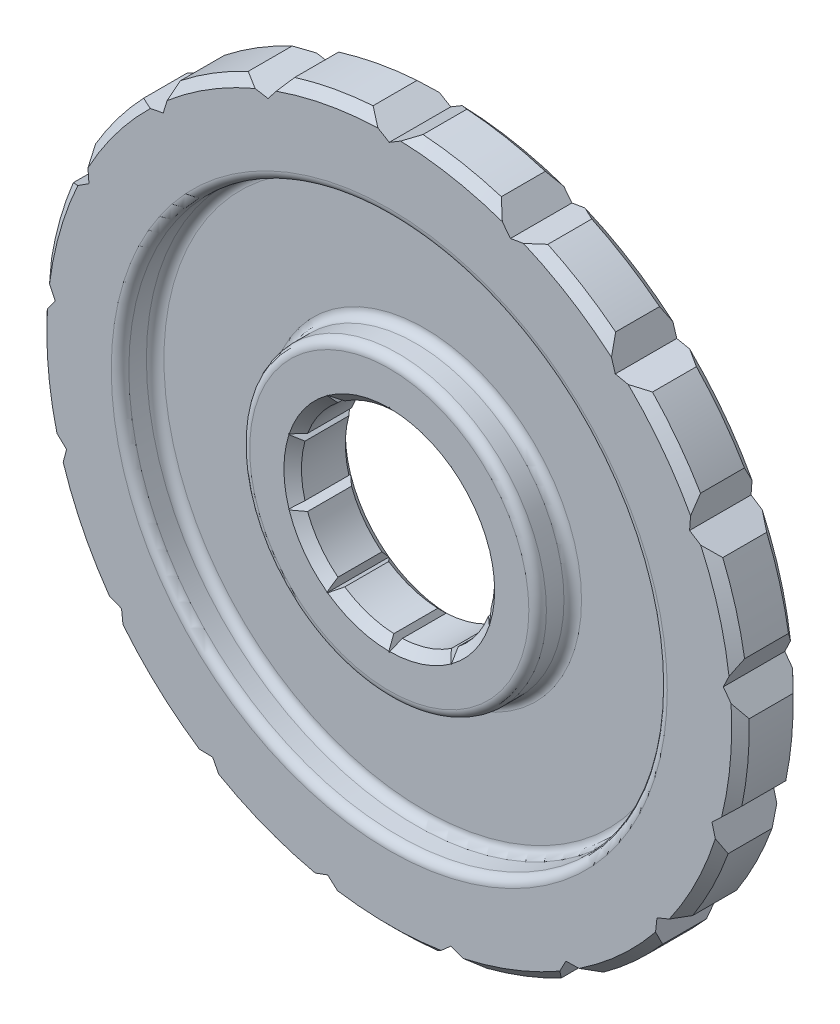
SolidWorks part; units mm, degrees
ref_plane "Front Plane" through (0, 0, 0) normal (0, 0, 1) x (1, 0, 0)
ref_plane "Top Plane" through (0, 0, 0) normal (0, 1, 0) x (1, 0, 0)
ref_plane "Right Plane" through (0, 0, 0) normal (1, 0, 0) x (0, 0, -1)
sketch "Sketch1" plane through (0, 0, 0) normal (0, 0, 1) x (1, 0, 0)
  circle A0 centre (0, 0) radius 11
  circle A1 centre (0, 0) radius 40
  dimension "D1" = 22
  dimension "D2" = 80
extrude "Boss-Extrude1" add sketch "Sketch1" along normal blind 7
chamfer "Chamfer1" distance 1 angle 45 4 edges at (40, 0, 0) (40, 0, 7) (11, 0, 0) (11, 0, 7)
sketch "Sketch2" plane through (0, 0, 7) normal (0, 0, 1) x (1, 0, 0)
  line L0 (0, 0) -> (0, 34.5062) construction
  line L1 (0, 12.1033) -> (-0.887, 10.0504)
  line L2 (-0.887, 10.0504) -> (0.887, 10.0504)
  line L3 (0.887, 10.0504) -> (0, 12.1033)
  line L4 (6.6251, 7.6096) -> (7.1141, 9.7917)
  line L5 (7.1141, 9.7917) -> (5.1899, 8.6523)
  line L6 (5.1899, 8.6523) -> (6.6251, 7.6096)
  line L7 (9.8326, 2.2622) -> (11.5109, 3.7401)
  line L8 (11.5109, 3.7401) -> (9.2844, 3.9493)
  line L9 (9.2844, 3.9493) -> (9.8326, 2.2622)
  line L10 (9.2844, -3.9493) -> (11.5109, -3.7401)
  line L11 (11.5109, -3.7401) -> (9.8326, -2.2622)
  line L12 (9.8326, -2.2622) -> (9.2844, -3.9493)
  line L13 (5.1899, -8.6523) -> (7.1141, -9.7917)
  line L14 (7.1141, -9.7917) -> (6.6251, -7.6096)
  line L15 (6.6251, -7.6096) -> (5.1899, -8.6523)
  line L16 (-0.887, -10.0504) -> (0, -12.1033)
  line L17 (0, -12.1033) -> (0.887, -10.0504)
  line L18 (0.887, -10.0504) -> (-0.887, -10.0504)
  line L19 (-6.6251, -7.6096) -> (-7.1141, -9.7917)
  line L20 (-7.1141, -9.7917) -> (-5.1899, -8.6523)
  line L21 (-5.1899, -8.6523) -> (-6.6251, -7.6096)
  line L22 (-9.8326, -2.2622) -> (-11.5109, -3.7401)
  line L23 (-11.5109, -3.7401) -> (-9.2844, -3.9493)
  line L24 (-9.2844, -3.9493) -> (-9.8326, -2.2622)
  line L25 (-9.2844, 3.9493) -> (-11.5109, 3.7401)
  line L26 (-11.5109, 3.7401) -> (-9.8326, 2.2622)
  line L27 (-9.8326, 2.2622) -> (-9.2844, 3.9493)
  line L28 (-5.1899, 8.6523) -> (-7.1141, 9.7917)
  line L29 (-7.1141, 9.7917) -> (-6.6251, 7.6096)
  line L30 (-6.6251, 7.6096) -> (-5.1899, 8.6523)
  line L31 (-4.9611, 41.1614) -> (0, 38.2086)
  line L32 (0, 38.2086) -> (4.9611, 41.1614)
  line L33 (4.9611, 41.1614) -> (-4.9611, 41.1614)
  line L34 (19.4954, 36.5897) -> (10.2431, 40.1741)
  line L35 (10.2431, 40.1741) -> (13.8025, 35.6284)
  line L36 (13.8025, 35.6284) -> (19.4954, 36.5897)
  line L37 (31.3966, 27.0764) -> (24.064, 33.761)
  line L38 (24.064, 33.761) -> (25.7409, 28.2365)
  line L39 (25.7409, 28.2365) -> (31.3966, 27.0764)
  line L40 (39.0576, 13.9062) -> (34.6348, 22.7883)
  line L41 (34.6348, 22.7883) -> (34.2029, 17.031)
  line L42 (34.2029, 17.031) -> (39.0576, 13.9062)
  line L43 (41.4436, -1.1421) -> (40.5281, 8.7379)
  line L44 (40.5281, 8.7379) -> (38.0456, 3.5254)
  line L45 (38.0456, 3.5254) -> (41.4436, -1.1421)
  line L46 (38.2324, -16.0361) -> (40.9478, -6.4926)
  line L47 (40.9478, -6.4926) -> (36.75, -10.4563)
  line L48 (36.75, -10.4563) -> (38.2324, -16.0361)
  line L49 (29.8578, -28.7644) -> (35.8373, -20.8462)
  line L50 (35.8373, -20.8462) -> (30.4911, -23.0258)
  line L51 (30.4911, -23.0258) -> (29.8578, -28.7644)
  line L52 (17.4507, -37.6079) -> (25.8868, -32.3845)
  line L53 (25.8868, -32.3845) -> (20.1142, -32.4856)
  line L54 (20.1142, -32.4856) -> (17.4507, -37.6079)
  line L55 (2.6867, -41.3722) -> (12.4401, -39.549)
  line L56 (12.4401, -39.549) -> (7.0208, -37.558)
  line L57 (7.0208, -37.558) -> (2.6867, -41.3722)
  line L58 (-12.4401, -39.549) -> (-2.6867, -41.3722)
  line L59 (-2.6867, -41.3722) -> (-7.0208, -37.558)
  line L60 (-7.0208, -37.558) -> (-12.4401, -39.549)
  line L61 (-25.8868, -32.3845) -> (-17.4507, -37.6079)
  line L62 (-17.4507, -37.6079) -> (-20.1142, -32.4856)
  line L63 (-20.1142, -32.4856) -> (-25.8868, -32.3845)
  line L64 (-35.8373, -20.8462) -> (-29.8578, -28.7644)
  line L65 (-29.8578, -28.7644) -> (-30.4911, -23.0258)
  line L66 (-30.4911, -23.0258) -> (-35.8373, -20.8462)
  line L67 (-40.9478, -6.4926) -> (-38.2324, -16.0361)
  line L68 (-38.2324, -16.0361) -> (-36.75, -10.4563)
  line L69 (-36.75, -10.4563) -> (-40.9478, -6.4926)
  line L70 (-40.5281, 8.7379) -> (-41.4436, -1.1421)
  line L71 (-41.4436, -1.1421) -> (-38.0456, 3.5254)
  line L72 (-38.0456, 3.5254) -> (-40.5281, 8.7379)
  line L73 (-34.6348, 22.7883) -> (-39.0576, 13.9062)
  line L74 (-39.0576, 13.9062) -> (-34.2029, 17.031)
  line L75 (-34.2029, 17.031) -> (-34.6348, 22.7883)
  line L76 (-24.064, 33.761) -> (-31.3966, 27.0764)
  line L77 (-31.3966, 27.0764) -> (-25.7409, 28.2365)
  line L78 (-25.7409, 28.2365) -> (-24.064, 33.761)
  line L79 (-10.2431, 40.1741) -> (-19.4954, 36.5897)
  line L80 (-19.4954, 36.5897) -> (-13.8025, 35.6284)
  line L81 (-13.8025, 35.6284) -> (-10.2431, 40.1741)
  point P36 (0, 0)
  point P88 (0, 0)
  dimension "D1" = 10
  dimension "D2" = 17
extrude "Cut-Extrude1" cut sketch "Sketch2" against normal blind 7
sketch "Sketch3" plane through (0, 0, 7) normal (0, 0, 1) x (1, 0, 0)
  circle A0 centre (0, 0) radius 16.8965
  circle A1 centre (0, 0) radius 30.6625
extrude "Cut-Extrude2" cut sketch "Sketch3" against normal blind 4
fillet "Fillet1" radius 1 4 edges at (30.6625, 0, 3) (16.8965, 0, 3) (30.6625, 0, 7) (16.8965, 0, 7)
